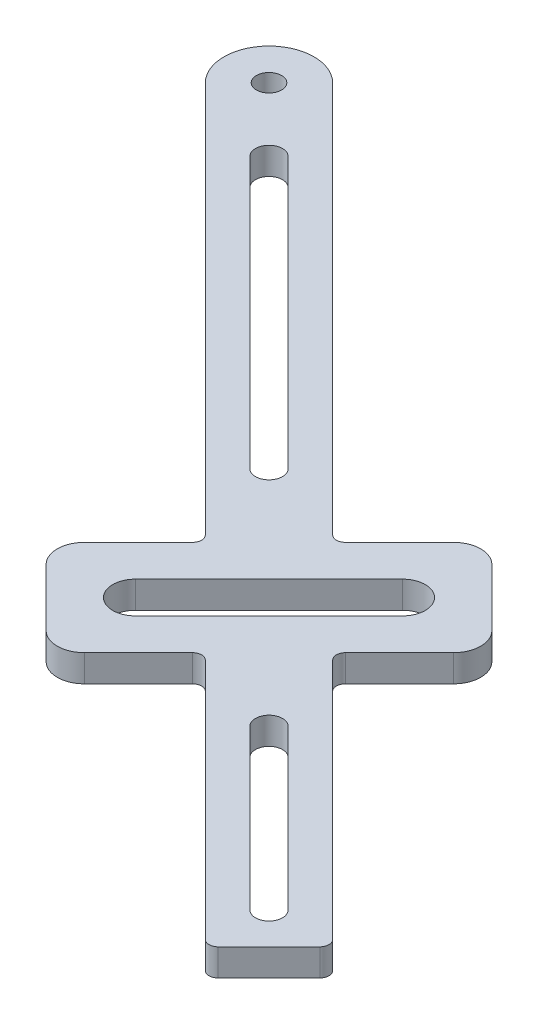
SolidWorks part; units mm, degrees
ref_plane "Front Plane" through (0, 0, 0) normal (0, 0, 1) x (1, 0, 0)
ref_plane "Top Plane" through (0, 0, 0) normal (0, 1, 0) x (1, 0, 0)
ref_plane "Right Plane" through (0, 0, 0) normal (1, 0, 0) x (0, 0, -1)
sketch "Sketch1" plane through (0, 0, 0) normal (0, 1, 0) x (1, 0, 0)
  line L16 (82.6259, -70.8778) -> (100.3035, -88.5555)
  line L17 (98.1822, -90.6768) -> (80.5045, -72.9992)
  line L18 (59.9984, -65.221) -> (74.8477, -50.3718)
  line L19 (78.3832, -53.9073) -> (63.534, -68.7565)
  line L20 (27.8251, -16.0771) -> (57.8771, -46.1291)
  line L21 (66.716, -50.0182) -> (23.2289, -6.5311)
  line L22 (16.1578, -13.6022) -> (59.6449, -57.0893)
  line L23 (59.6449, -58.5035) -> (53.6345, -64.5139)
  line L24 (53.6345, -68.7565) -> (59.9984, -75.1205)
  line L25 (64.2411, -75.1205) -> (70.2515, -69.1101)
  line L26 (71.6657, -69.1101) -> (98.5358, -95.9801)
  line L27 (99.95, -95.9801) -> (105.6068, -90.3233)
  line L28 (105.6068, -88.9091) -> (78.7368, -62.039)
  line L29 (78.7368, -60.6248) -> (84.7472, -54.6144)
  line L30 (84.7472, -50.3718) -> (78.3832, -44.0078)
  line L31 (74.1406, -44.0078) -> (68.1302, -50.0182)
  line L32 (55.7558, -48.2504) -> (25.7038, -18.1984)
  line L33 (26.7644, -17.1377) -> (99.2429, -89.6162) construction
  line L34 (76.6155, -52.1395) -> (61.7662, -66.9888) construction
  line L35 (74.8477, -50.3718) -> (78.3832, -53.9073) construction
  line L36 (59.9984, -65.221) -> (63.534, -68.7565) construction
  arc A45 (82.6259, -70.8778) -> (80.5045, -72.9992) centre (81.5652, -71.9385) ccw
  arc A46 (98.1822, -90.6768) -> (100.3035, -88.5555) centre (99.2429, -89.6162) ccw
  arc A47 (78.3832, -53.9073) -> (74.8477, -50.3718) centre (76.6155, -52.1395) ccw
  arc A48 (59.9984, -65.221) -> (63.534, -68.7565) centre (61.7662, -66.9888) ccw
  arc A49 (23.2289, -6.5311) -> (16.1578, -13.6022) centre (19.6934, -10.0667) ccw
  arc A50 (59.6449, -58.5035) -> (59.6449, -57.0893) centre (58.9378, -57.7964) ccw
  arc A51 (53.6345, -64.5139) -> (53.6345, -68.7565) centre (55.7558, -66.6352) ccw
  arc A52 (59.9984, -75.1205) -> (64.2411, -75.1205) centre (62.1198, -72.9992) ccw
  arc A53 (71.6657, -69.1101) -> (70.2515, -69.1101) centre (70.9586, -69.8172) ccw
  arc A54 (98.5358, -95.9801) -> (99.95, -95.9801) centre (99.2429, -95.273) ccw
  arc A55 (105.6068, -90.3233) -> (105.6068, -88.9091) centre (104.8997, -89.6162) ccw
  arc A56 (78.7368, -60.6248) -> (78.7368, -62.039) centre (79.4439, -61.3319) ccw
  arc A57 (84.7472, -54.6144) -> (84.7472, -50.3718) centre (82.6259, -52.4931) ccw
  arc A58 (78.3832, -44.0078) -> (74.1406, -44.0078) centre (76.2619, -46.1291) ccw
  arc A59 (66.716, -50.0182) -> (68.1302, -50.0182) centre (67.4231, -49.3111) ccw
  arc A60 (55.7558, -48.2504) -> (57.8771, -46.1291) centre (56.8165, -47.1898) ccw
  arc A61 (27.8251, -16.0771) -> (25.7038, -18.1984) centre (26.7644, -17.1377) ccw
  circle A62 centre (19.6934, -10.0667) radius 1.4
  point P1 (69.1908, -59.5641)
  dimension "D2" = 5
  dimension "D3" = 2.8
  dimension "D1" = 61.5
  dimension "D4" = 2.5
  dimension "D6" = 2.5
  dimension "D5" = 21
extrude "Boss-Extrude1" add sketch "Sketch1" along normal blind 3
